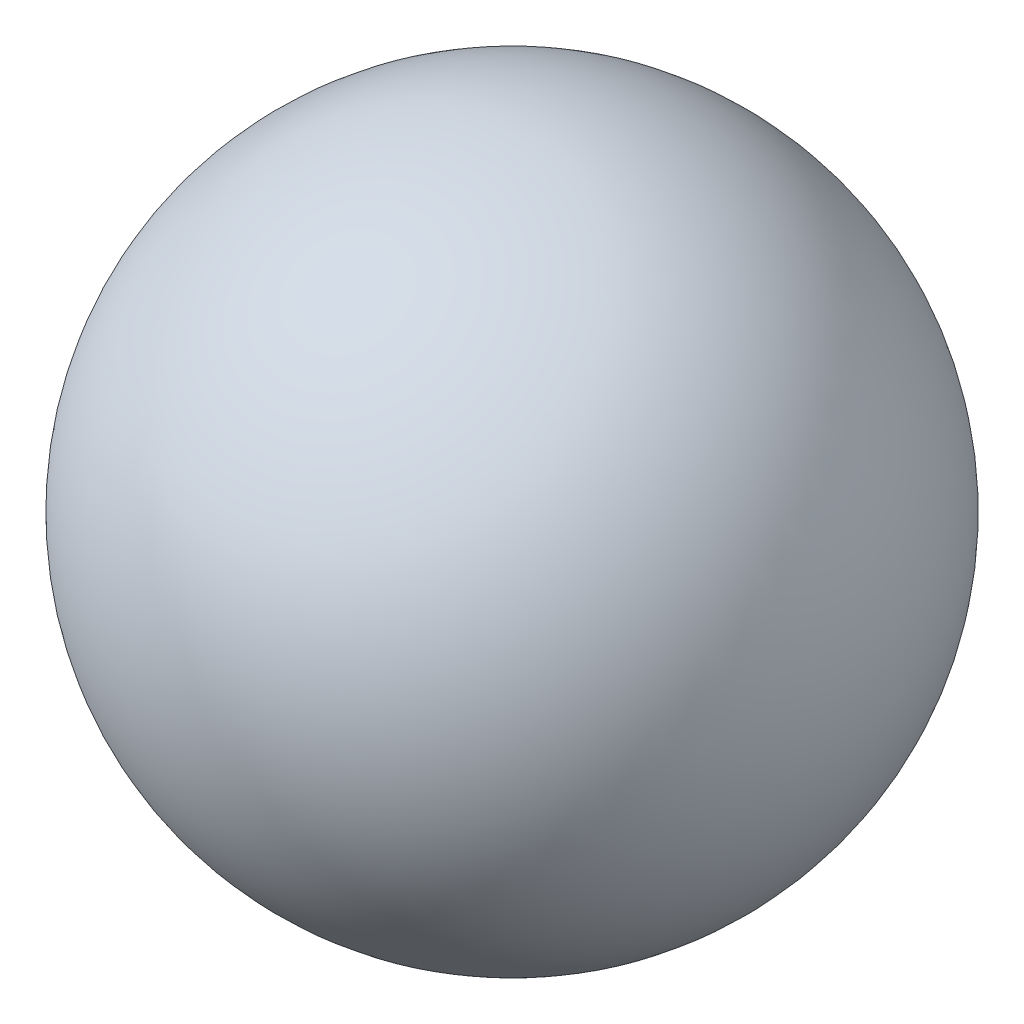
SolidWorks part; units mm, degrees
ref_plane "Plan de face" through (0, 0, 0) normal (0, 0, 1) x (1, 0, 0)
ref_plane "Plan de dessus" through (0, 0, 0) normal (0, 1, 0) x (1, 0, 0)
ref_plane "Plan de droite" through (0, 0, 0) normal (1, 0, 0) x (0, 0, -1)
sketch "Esquisse1" plane through (0, 0, 0) normal (0, 0, 1) x (1, 0, 0)
  line L0 (0, 1.5) -> (0, -1.5)
  arc A0 (0, 1.5) -> (0, -1.5) centre (0, 0) ccw
  dimension "D1" = 3
revolve "Révolution2" add sketch "Esquisse1" angle 360 about L0
sketch "Esquisse2" plane through (0, 0, 0) normal (0, 0, 1) x (1, 0, 0)
  point P0 (0, 0)
